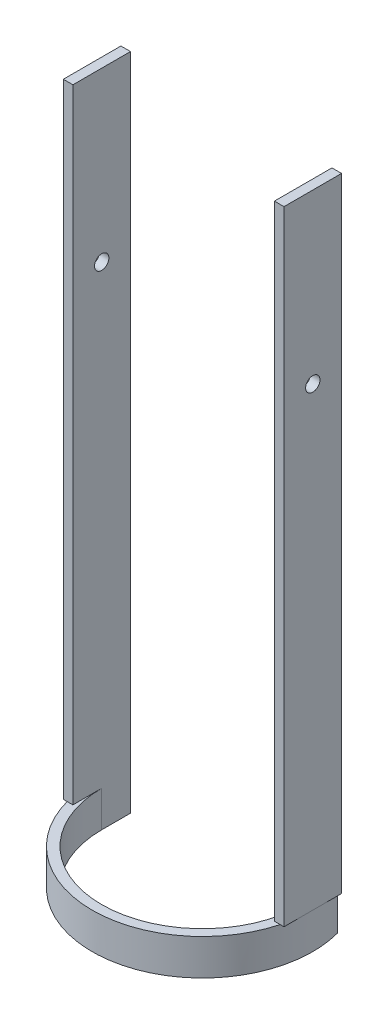
SolidWorks part; units mm, degrees
ref_plane "Front" through (0, 0, 0) normal (0, 0, 1) x (1, 0, 0)
ref_plane "Top" through (0, 0, 0) normal (0, 1, 0) x (1, 0, 0)
ref_plane "Right" through (0, 0, 0) normal (1, 0, 0) x (0, 0, -1)
sketch "草图1" plane through (0, 0, 0) normal (0, 1, 0) x (1, 0, 0)
  line L0 (-42, 0) -> (0, 0) construction
  line L1 (-46, 0) -> (-84.254, 0) construction
  line L2 (0, 0) -> (0, 41.4) construction
  line L5 (-46, 0) -> (-46, 12)
  line L6 (-46, 12) -> (-42, 12)
  line L7 (-42, 0) -> (-42, 12)
  line L11 (46, 0) -> (46, 12)
  line L12 (46, 12) -> (42, 12)
  line L13 (42, 0) -> (42, 12)
  arc A2 (-46, 0) -> (46, 0) centre (0, 0) ccw
  arc A3 (-42, 0) -> (42, 0) centre (0, 0) ccw
  dimension "D1" = 12
  dimension "D2" = 12
extrude "凸台-拉伸1" add sketch "草图1" along normal blind 30
sketch "草图2" plane through (0, 30, 0) normal (0, 1, 0) x (1, 0, 0)
  line L9 (-46, 12) -> (-42, 12)
  line L10 (-46, 12) -> (-46, -12)
  line L11 (-46, -12) -> (-42, -12)
  line L12 (-42, 12) -> (-42, -12)
  line L13 (46, 12) -> (42, 12)
  line L14 (46, 12) -> (46, -12)
  line L15 (46, -12) -> (42, -12)
  line L16 (42, 12) -> (42, -12)
  dimension "D1" = 24
  dimension "D2" = 4
  dimension "D3" = 4
  dimension "D4" = 24
sketch "草图4" plane through (0, 30, 0) normal (0, 1, 0) x (1, 0, 0)
  line L1 (46, 12) -> (42, 12)
  line L2 (46, 12) -> (46, -12)
  line L3 (46, -12) -> (42, -12)
  line L4 (42, 12) -> (42, -12)
  line L5 (-46, 12) -> (-42, 12)
  line L6 (-46, 12) -> (-46, -12)
  line L7 (-46, -12) -> (-42, -12)
  line L8 (-42, 12) -> (-42, -12)
  dimension "D1" = 4
  dimension "D2" = 24
  dimension "D3" = 4
  dimension "D4" = 24
extrude "凸台-拉伸3" add sketch "草图4" along normal blind 260
sketch "草图7" plane through (0, 0, -12) normal (0, 0, -1) x (-1, 0, 0)
  line L1 (-66.6226, 15) -> (82.9745, 15)
  line L2 (-66.6226, 15) -> (-66.6226, -100.9415)
  line L3 (-66.6226, -100.9415) -> (82.9745, -100.9415)
  line L4 (82.9745, 15) -> (82.9745, -100.9415)
  dimension "D1" = 15
extrude "切除-拉伸3" cut sketch "草图7" against normal through all
sketch "草图9" plane through (46, 0, 0) normal (1, 0, 0) x (0, 0, -1)
  circle A0 centre (0, 220) radius 3
extrude "切除-拉伸5" cut sketch "草图9" against normal through all
sketch "草图10" plane through (0, 15, 0) normal (0, -1, 0) x (1, 0, 0)
  circle A0 centre (0, 0) radius 46
  circle A1 centre (0, 0) radius 50
extrude "切除-拉伸6" cut sketch "草图10" against normal blind 15
